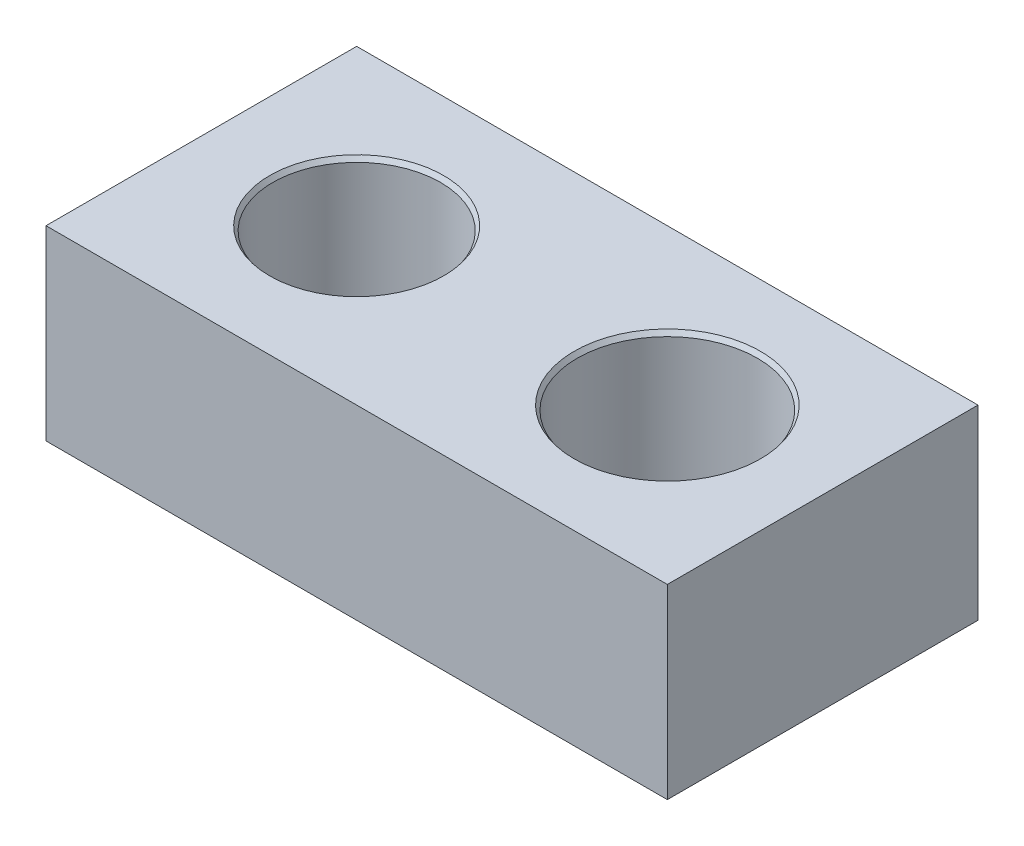
SolidWorks part; units mm, degrees
ref_plane "Front Plane" through (0, 0, 0) normal (0, 0, 1) x (1, 0, 0)
ref_plane "Top Plane" through (0, 0, 0) normal (0, 1, 0) x (1, 0, 0)
ref_plane "Right Plane" through (0, 0, 0) normal (1, 0, 0) x (0, 0, -1)
sketch "Sketch1" plane through (0, 0, 0) normal (0, 1, 0) x (1, 0, 0)
  line L0 (0, 5) -> (20, 5) construction
  line L1 (0, 0) -> (20, 0)
  line L2 (0, 0) -> (0, 10)
  line L3 (0, 10) -> (20, 10)
  line L4 (20, 0) -> (20, 10)
  dimension "D1" = 10
  dimension "D2" = 20
extrude "Boss-Extrude1" add sketch "Sketch1" along normal blind 6
hole_wizard "Ø5.4 (5.4) Diameter Hole1" positions "Sketch2" profile "Sketch3" hole size "Ø5.4" standard "ANSI Metric" end condition through all
sketch "Sketch2" plane through (0, 6, 0) normal (0, 1, 0) x (1, 0, 0)
  line L0 (0, 10) -> (0, 0) construction
  point P0 (5, 5)
  dimension "D1" = 5
sketch "Sketch3" plane through (5, 6, -5) normal (1, 0, 0) x (0, 0, 1)
  line L0 (0, 0) -> (0, 6)
  line L1 (0, 6) -> (2.7, 6)
  line L2 (2.7, 6) -> (2.7, 0.1428)
  line L3 (2.7, 0.1428) -> (2.8, 0)
  line L5 (2.8, 0) -> (0, 0)
  line L6 (-2.7, 0.1428) -> (-2.8, 0) construction
  line L11 (0, -6.35) -> (0, 107.95) construction
  dimension "Thru Hole Dia." = 5.4
  dimension "Thru Hole Depth" = 6
  dimension "Near C'Sink Dia." = 5.6
  dimension "Near C'Sink Angle" = 70
hole_wizard "Ø5.8 (5.8) Diameter Hole1" positions "Sketch4" profile "Sketch5" hole size "Ø5.8" standard "ANSI Metric" end condition through all
sketch "Sketch4" plane through (0, 6, 0) normal (0, 1, 0) x (1, 0, 0)
  line L0 (20, 0) -> (20, 10) construction
  point P0 (15, 5)
  dimension "D1" = 5
sketch "Sketch5" plane through (15, 6, -5) normal (1, 0, 0) x (0, 0, 1)
  line L0 (0, 0) -> (0, 6)
  line L1 (0, 6) -> (2.9, 6)
  line L2 (2.9, 6) -> (2.9, 0.1428)
  line L3 (2.9, 0.1428) -> (3, 0)
  line L5 (3, 0) -> (0, 0)
  line L6 (-2.9, 0.1428) -> (-3, 0) construction
  line L11 (0, -6.35) -> (0, 107.95) construction
  dimension "Thru Hole Dia." = 5.8
  dimension "Thru Hole Depth" = 6
  dimension "Near C'Sink Dia." = 6
  dimension "Near C'Sink Angle" = 70
